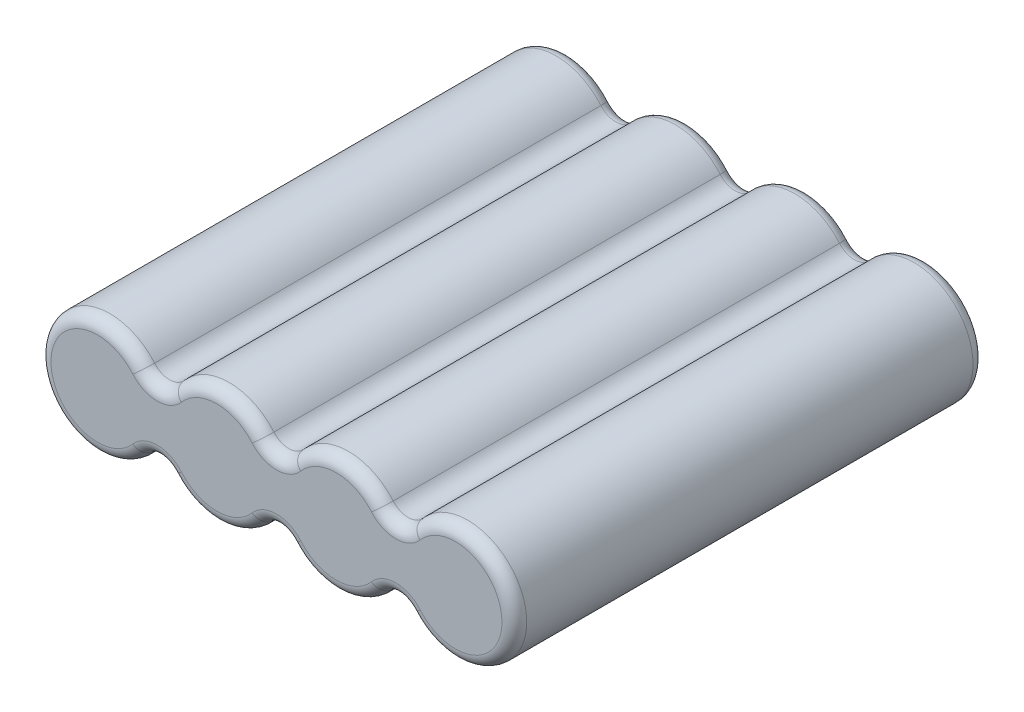
SolidWorks part; units mm, degrees
ref_plane "Front Plane" through (0, 0, 0) normal (0, 0, 1) x (1, 0, 0)
ref_plane "Top Plane" through (0, 0, 0) normal (0, 1, 0) x (1, 0, 0)
ref_plane "Right Plane" through (0, 0, 0) normal (1, 0, 0) x (0, 0, -1)
sketch "Sketch1" plane through (0, 0, 0) normal (0, 0, 1) x (1, 0, 0)
  line L0 (0, 0) -> (28.956, 0) construction
  arc A0 (3.6195, 3.0953) -> (3.6195, -3.0953) centre (0, 0) ccw
  arc A1 (6.0325, -3.0953) -> (13.2715, -3.0953) centre (9.652, 0) ccw
  arc A2 (15.6845, -3.0953) -> (22.9235, -3.0953) centre (19.304, 0) ccw
  arc A3 (25.3365, -3.0953) -> (25.3365, 3.0953) centre (28.956, 0) ccw
  arc A4 (3.6195, 3.0953) -> (6.0325, 3.0953) centre (4.826, 4.127) ccw
  arc A5 (3.6195, -3.0953) -> (6.0325, -3.0953) centre (4.826, -4.127) cw
  arc A6 (13.2715, 3.0953) -> (15.6845, 3.0953) centre (14.478, 4.127) ccw
  arc A7 (13.2715, -3.0953) -> (15.6845, -3.0953) centre (14.478, -4.127) cw
  arc A8 (22.9235, 3.0953) -> (25.3365, 3.0953) centre (24.13, 4.127) ccw
  arc A9 (22.9235, -3.0953) -> (25.3365, -3.0953) centre (24.13, -4.127) cw
  arc A10 (13.2715, 3.0953) -> (6.0325, 3.0953) centre (9.652, 0) ccw
  arc A11 (22.9235, 3.0953) -> (15.6845, 3.0953) centre (19.304, 0) ccw
  dimension "D1" = 9.525
  dimension "D3" = 3.175
  dimension "D2" = 4
  dimension "D4" = 3
extrude "Boss-Extrude1" add sketch "Sketch1" along normal blind 38.1
fillet "Fillet2" radius 1 24 edges at (4.826, 2.5395, 38.1) (9.652, 4.7625, 38.1) (14.478, 2.5395, 38.1) (19.304, 4.7625, 38.1) (24.13, 2.5395, 38.1) (33.7185, 0, 38.1) (24.13, -2.5395, 38.1) (19.304, -4.7625, 38.1) (14.478, -2.5395, 38.1) (9.652, -4.7625, 38.1) (4.826, -2.5395, 38.1) (4.826, 2.5395, 0) (9.652, 4.7625, 0) (14.478, 2.5395, 0) (19.304, 4.7625, 0) (24.13, 2.5395, 0) (33.7185, 0, 0) (24.13, -2.5395, 0) (19.304, -4.7625, 0) (14.478, -2.5395, 0) (9.652, -4.7625, 0) (4.826, -2.5395, 0) (-4.7625, 0, 38.1) (-4.7625, 0, 0)
